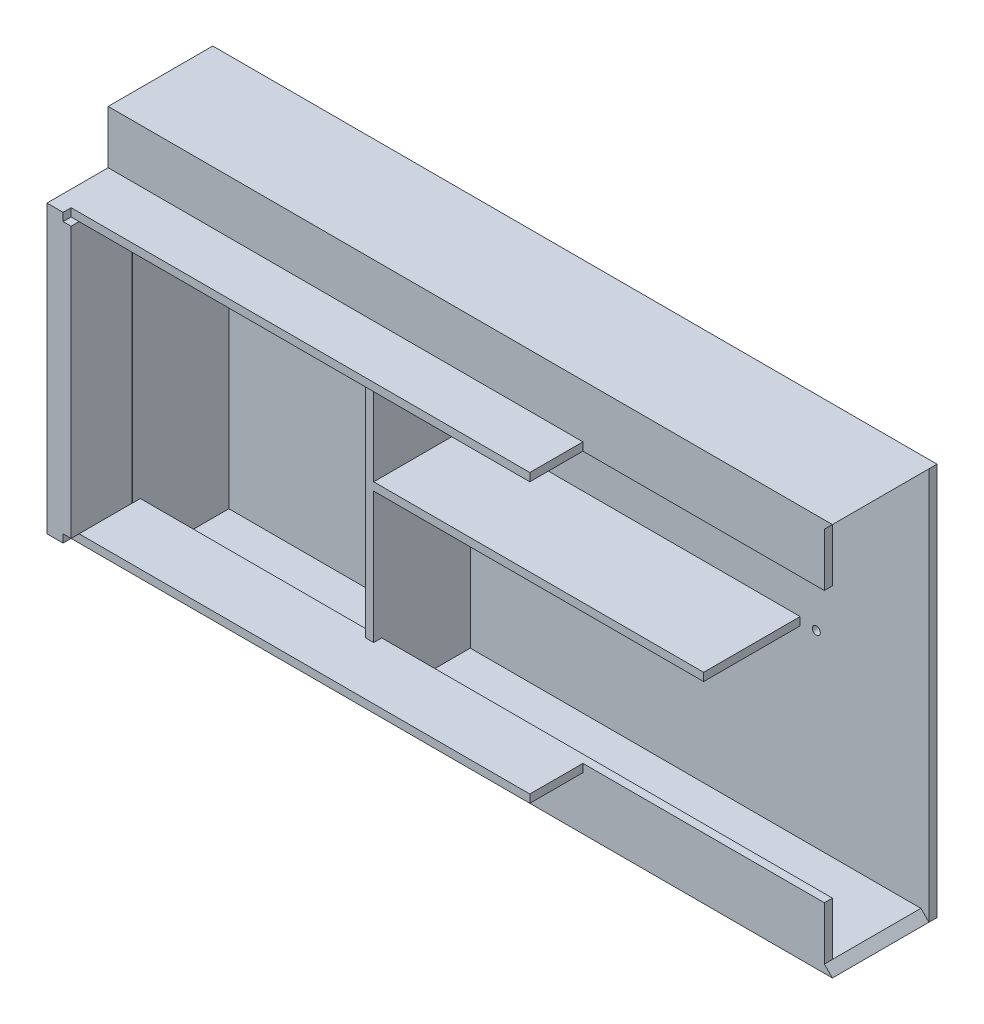
SolidWorks part; units mm, degrees
ref_plane "Front Plane" through (0, 0, 0) normal (0, 0, 1) x (1, 0, 0)
ref_plane "Top Plane" through (0, 0, 0) normal (0, 1, 0) x (1, 0, 0)
ref_plane "Right Plane" through (0, 0, 0) normal (1, 0, 0) x (0, 0, -1)
sketch "Sketch1" plane through (0, 0, 0) normal (0, 0, 1) x (1, 0, 0)
  line L1 (-220, -122) -> (220, -122)
  line L2 (-220, -122) -> (-220, 122)
  line L3 (-220, 122) -> (220, 122)
  line L4 (220, -122) -> (220, 122)
  line L5 (-220, -122) -> (220, 122) construction
  line L6 (-220, 122) -> (220, -122) construction
  line L7 (-130, -102) -> (-70, -102)
  line L8 (-130, -102) -> (-130, 102)
  line L9 (-130, 102) -> (-70, 102)
  line L10 (-70, -102) -> (-70, 102)
  line L11 (-130, -102) -> (-70, 102) construction
  line L12 (-130, 102) -> (-70, -102) construction
  point P0 (0, 0)
  point P6 (-100, 0)
  dimension "D1" = 244
  dimension "D2" = 440
  dimension "D3" = 90
  dimension "D4" = 204
  dimension "D5" = 60
extrude "Boss-Extrude1" add sketch "Sketch1" along normal blind 5
sketch "Sketch2" plane through (0, 0, 5) normal (0, 0, 1) x (1, 0, 0)
  line L0 (-215, -117) -> (215, -117)
  line L1 (215, 117) -> (220, 122)
  line L2 (215, 117) -> (-215, 117)
  line L3 (-215, 117) -> (-215, -117)
  line L4 (220, -122) -> (220, 122)
  line L5 (220, 122) -> (-220, 122)
  line L6 (-220, 122) -> (-220, -122)
  line L7 (-220, -122) -> (220, -122)
  line L8 (215, -117) -> (220, -122)
  line L9 (220, 122) -> (-220, 122)
  line L10 (-220, 122) -> (-220, -122)
  line L11 (-220, -122) -> (220, -122)
  line L12 (220, -122) -> (220, 122) construction
  line L13 (215, -117) -> (215, 117) construction
  dimension "D1" = 0
  dimension "D2" = 5
extrude "Boss-Extrude2" add sketch "Sketch2" along normal blind 60
sketch "Sketch3" plane through (-220, 0, 0) normal (-1, 0, 0) x (0, 0, 1)
  line L4 (0, 122) -> (0, -122)
  line L5 (0, -122) -> (65, -122)
  line L6 (65, -122) -> (65, 122)
  line L7 (65, 122) -> (0, 122)
  line L8 (0, 122) -> (0, -122)
  line L9 (0, -122) -> (65, -122)
  line L10 (65, -122) -> (65, 122)
  line L11 (65, 122) -> (0, 122)
  dimension "D1" = 0
extrude "Boss-Extrude3" add sketch "Sketch3" along normal blind 10
sketch "Sketch9" plane through (0, -117, 0) normal (0, 1, 0) x (1, 0, 0)
  line L0 (-215, -65) -> (-215, -5) construction
  line L1 (215, -65) -> (-215, -65)
  line L2 (215, -65) -> (215, -60)
  line L3 (215, -60) -> (-215, -60)
  line L4 (-215, -65) -> (-215, -60)
  dimension "D1" = 5
extrude "Boss-Extrude6" add sketch "Sketch9" along normal blind 33
sketch "Sketch10" plane through (0, 0, 65) normal (0, 0, 1) x (1, 0, 0)
  line L0 (-230, -122) -> (-230, 122) construction
  line L1 (215, -84) -> (-215.0425, -84)
  line L2 (215, -84) -> (215, -89)
  line L3 (215, -89) -> (-215.0425, -89)
  line L5 (220, 122) -> (-230, 122) construction
  line L6 (-230, -89) -> (-215.0425, -89)
  line L7 (-230, -89) -> (-230, 122)
  line L8 (-230, 122) -> (-215.0425, 122)
  line L9 (-215.0425, -84) -> (-215.0425, 122)
extrude "Boss-Extrude7" add sketch "Sketch10" along normal blind 38
mirror "Mirror4" about plane through (0, 0, 0) normal (0, 1, 0) of "Boss-Extrude7", "Boss-Extrude6"
sketch "Sketch11" plane through (-215.0425, 0, 0) normal (1, 0, 0) x (0, 0, -1)
  line L0 (-103, 122) -> (-103, 89) construction
  line L1 (-103, 89) -> (-65, 89) construction
  line L2 (-65, 89) -> (-65, 122) construction
  line L3 (-65, 122) -> (-103, 122) construction
  line L4 (-65, -89) -> (-103, -89) construction
  line L5 (-103, -89) -> (-103, -122) construction
  line L6 (-103, -122) -> (-65, -122) construction
  line L7 (-65, -122) -> (-65, -89) construction
  line L8 (-103, 122) -> (-103, 89)
  line L9 (-103, 89) -> (-65, 89)
  line L10 (-65, 89) -> (-65, 122)
  line L11 (-65, 122) -> (-103, 122)
  line L12 (-65, -89) -> (-103, -89)
  line L13 (-103, -89) -> (-103, -122)
  line L14 (-103, -122) -> (-65, -122)
  line L15 (-65, -122) -> (-65, -89)
extrude "Cut-Extrude3" cut sketch "Sketch11" against normal blind 38
sketch "Sketch12" plane through (-230, 0, 0) normal (-1, 0, 0) x (0, 0, 1)
  line L0 (0, 0) -> (103, 0) construction
  line L1 (103, 89) -> (103, -89) construction
  line L2 (44.5, 25) -> (44.5, -25)
  line L3 (31.5, -25) -> (44.5, -25)
  line L4 (31.5, -25) -> (31.5, 25)
  line L5 (31.5, 25) -> (44.5, 25)
  line L6 (71.5, -25) -> (71.5, 25)
  line L7 (31.5, -25) -> (71.5, 25) construction
  line L8 (31.5, 25) -> (71.5, -25) construction
  line L9 (58.5, 25) -> (58.5, -25)
  line L10 (58.5, -25) -> (71.5, -25)
  line L11 (58.5, 25) -> (71.5, 25)
  point P5 (51.5, 0)
  dimension "D1" = 40
  dimension "D2" = 13
  dimension "D3" = 13
  dimension "D4" = 50
extrude "Cut-Extrude4" cut sketch "Sketch12" against normal blind 10 draft 30
sketch "Sketch14" plane through (0, 0, 0) normal (0, 1, 0) x (1, 0, 0)
  line L0 (-230, -71.5) -> (-219.0222, -54.5)
  line L1 (-219.0222, -54.5) -> (-230, -58.5)
  line L2 (-230, -58.5) -> (-230, -71.5)
  line L3 (-230, -31.5) -> (-219.0222, -48.5)
  line L4 (-219.0222, -48.5) -> (-230, -44.5)
  line L5 (-230, -31.5) -> (-230, -44.5)
  dimension "D1" = 17
  dimension "D2" = 17
extrude "Cut-Extrude6" cut sketch "Sketch14" against normal mid plane 60
sketch "Sketch16" plane through (215, 0, 0) normal (1, 0, 0) x (0, 0, -1)
  line L0 (-103, -84) -> (-60, -84) construction
  line L1 (-103, -89) -> (-98, -89)
  line L2 (-103, -89) -> (-103, -84)
  line L3 (-103, -84) -> (-98, -84)
  line L4 (-98, -89) -> (-98, -84)
  line L5 (-103, 89) -> (-65, 89) construction
  line L6 (-103, 84) -> (-98, 84)
  line L7 (-103, 84) -> (-103, 89)
  line L8 (-103, 89) -> (-98, 89)
  line L9 (-98, 84) -> (-98, 89)
  dimension "D1" = 5
  dimension "D2" = 5
extrude "Cut-Extrude7" cut sketch "Sketch16" against normal blind 435
sketch "Sketch17" plane through (0, 0, 5) normal (0, 0, 1) x (1, 0, 0)
  line L0 (-215, 117) -> (215, 117) construction
  line L1 (-70, 117) -> (-65, 117)
  line L2 (-70, 117) -> (-70, -117)
  line L3 (-70, -117) -> (-65, -117)
  line L4 (-65, 117) -> (-65, -117)
  line L5 (215, -117) -> (-215, -117) construction
  line L6 (-70, -102) -> (-70, 102) construction
  dimension "D1" = 5
extrude "Boss-Extrude8" add sketch "Sketch17" along normal blind 60
sketch "Sketch18" plane through (0, 0, 5) normal (0, 0, 1) x (1, 0, 0)
  line L0 (140, 2.5) -> (140, -2.5)
  line L1 (-70, 0) -> (140, 0) construction
  line L2 (-70, 84) -> (-70, -84) construction
  line L4 (140, -2.5) -> (-70, -2.5)
  line L5 (-70, -2.5) -> (-70, 2.5)
  line L6 (140, 2.5) -> (-70, 2.5)
  line L8 (140, -1.0623) -> (-70, -4.6554) construction
  line L9 (140, 0.576) -> (-70, 4.6554) construction
  point P0 (184.8402, -0.2951)
  dimension "D1" = 5
  dimension "D2" = 210
extrude "Boss-Extrude9" add sketch "Sketch18" along normal blind 60
sketch "Sketch19" plane through (0, 0, 5) normal (0, 0, 1) x (1, 0, 0)
  line L0 (0, 0) -> (150, 0) construction
  circle A0 centre (150, 0) radius 2.5
  dimension "D1" = 5
  dimension "D2" = 10
extrude "Cut-Extrude8" cut sketch "Sketch19" against normal blind 50
sketch "Sketch22" plane through (215, 0, 0) normal (1, 0, 0) x (0, 0, -1)
  line L1 (-65, -89) -> (-98, -89)
  line L2 (-65, -89) -> (-65, -84)
  line L3 (-65, -84) -> (-98, -84)
  line L4 (-98, -89) -> (-98, -84)
  line L5 (-65, 89) -> (-98, 89)
  line L6 (-65, 89) -> (-65, 84)
  line L7 (-65, 84) -> (-98, 84)
  line L8 (-98, 89) -> (-98, 84)
extrude "Cut-Extrude10" cut sketch "Sketch22" against normal blind 150
